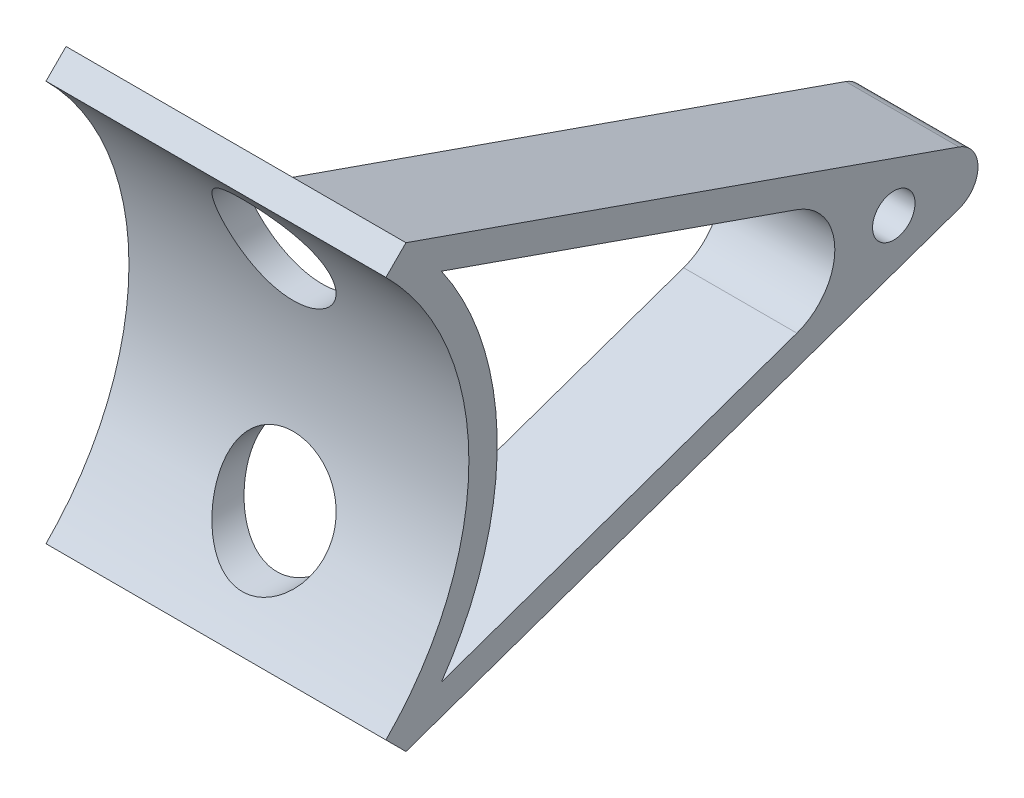
SolidWorks part; units mm, degrees
material "Chrome Stainless Steel"
ref_plane "Front Plane" through (0, 0, 0) normal (0, 0, 1) x (1, 0, 0)
ref_plane "Top Plane" through (0, 0, 0) normal (0, 1, 0) x (1, 0, 0)
ref_plane "Right Plane" through (0, 0, 0) normal (1, 0, 0) x (0, 0, -1)
sketch "Sketch1" plane through (0, 0, 0) normal (1, 0, 0) x (0, 0, -1)
  line L0 (-950.7492, 0) -> (46586.7085, 0) construction
  line L1 (70.7107, 70.7107) -> (77.7817, 77.7817)
  line L2 (0, -950.7492) -> (0, 46586.7085) construction
  line L3 (70.7107, -70.7107) -> (77.7817, -77.7817)
  arc A0 (70.7107, 70.7107) -> (70.7107, -70.7107) centre (0, 0) cw
  arc A1 (77.7817, 77.7817) -> (77.7817, -77.7817) centre (0, 0) cw
  dimension "D1" = 100
  dimension "D2" = 10
extrude "Boss-Extrude1" add sketch "Sketch1" along normal blind 120
sketch "Sketch2" plane through (120, 0, 0) normal (1, 0, 0) x (0, 0, -1)
  line L0 (77.7817, 77.7817) -> (273.0347, 9.4385)
  line L1 (273.0347, -9.4385) -> (77.7817, -77.7817)
  line L2 (77.7817, 67.1869) -> (215.8003, 18.877)
  line L3 (215.8003, -18.877) -> (77.7817, -67.1869)
  line L4 (269.731, 0) -> (74.478, -68.3432) construction
  line L5 (74.478, 68.3432) -> (269.731, 0) construction
  line L6 (77.7817, 77.7817) -> (77.7817, 67.1869)
  line L7 (77.7817, -77.7817) -> (77.7817, -67.1869)
  arc A0 (273.0347, 9.4385) -> (273.0347, -9.4385) centre (269.731, 0) cw
  arc A2 (215.8003, -18.877) -> (215.8003, 18.877) centre (209.1929, 0) ccw
  arc A3 (269.731, 0) -> (269.731, 0) centre (269.731, 0) cw construction
  point P8 (300, 0)
  dimension "D2" = 10
  dimension "D4" = 20
  dimension "D1" = 300
  dimension "D3" = 10
extrude "Boss-Extrude2" add sketch "Sketch2" against normal blind 40
sketch "Sketch4" plane through (120, 0, 0) normal (1, 0, 0) x (0, 0, -1)
  circle A0 centre (250, 0) radius 7.5
  dimension "D1" = 15
  dimension "D2" = 250
extrude "Cut-Extrude1" cut sketch "Sketch4" against normal blind 40
sketch "Sketch6" plane through (0, 0, 0) normal (0, 0, 1) x (1, 0, 0)
  circle A0 centre (60, 40) radius 20
  circle A1 centre (60, -40) radius 20
  dimension "D1" = 40
  dimension "D2" = 80
  dimension "D3" = 40
  dimension "D4" = 60
extrude "Cut-Extrude2" cut sketch "Sketch6" against normal through all
